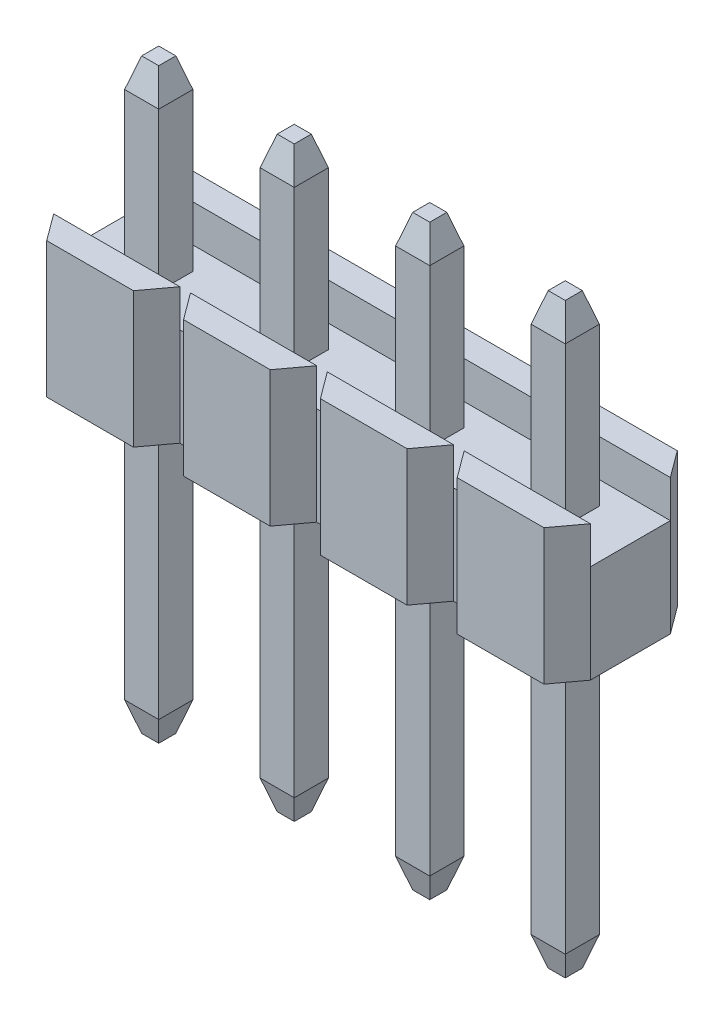
SolidWorks part; units mm, degrees
material "Plain Carbon Steel"
ref_plane "Front Plane" through (0, 0, 0) normal (0, 0, 1) x (1, 0, 0)
ref_plane "Top Plane" through (0, 0, 0) normal (0, 1, 0) x (1, 0, 0)
ref_plane "Right Plane" through (0, 0, 0) normal (1, 0, 0) x (0, 0, -1)
sketch "Sketch1" plane through (0, 0, 0) normal (0, 1, 0) x (1, 0, 0)
  line L0 (-4.66, -1.25) -> (-3.035, -1.25)
  line L1 (-3.035, -1.25) -> (-2.665, -0.75)
  line L2 (-2.665, -0.75) -> (-2.465, -0.75)
  line L3 (-2.465, -0.75) -> (-2.095, -1.25)
  line L4 (-2.095, -1.25) -> (-0.47, -1.25)
  line L5 (-0.47, -1.25) -> (-0.1, -0.75)
  line L6 (-0.1, -0.75) -> (0.1, -0.75)
  line L7 (0.1, -0.75) -> (0.47, -1.25)
  line L8 (0.47, -1.25) -> (2.095, -1.25)
  line L9 (2.095, -1.25) -> (2.465, -0.75)
  line L10 (2.465, -0.75) -> (2.665, -0.75)
  line L11 (2.665, -0.75) -> (3.035, -1.25)
  line L12 (3.035, -1.25) -> (4.66, -1.25)
  line L13 (4.66, -1.25) -> (5.03, -0.75)
  line L14 (5.03, -0.75) -> (5.03, 0.75)
  line L15 (5.03, 0.75) -> (4.66, 1.25)
  line L16 (4.66, 1.25) -> (3.035, 1.25)
  line L17 (3.035, 1.25) -> (2.665, 0.75)
  line L18 (2.665, 0.75) -> (2.465, 0.75)
  line L19 (2.465, 0.75) -> (2.095, 1.25)
  line L20 (2.095, 1.25) -> (0.47, 1.25)
  line L21 (0.47, 1.25) -> (0.1, 0.75)
  line L22 (0.1, 0.75) -> (-0.1, 0.75)
  line L23 (-0.1, 0.75) -> (-0.47, 1.25)
  line L24 (-0.47, 1.25) -> (-2.095, 1.25)
  line L25 (-2.095, 1.25) -> (-2.465, 0.75)
  line L26 (-2.465, 0.75) -> (-2.665, 0.75)
  line L27 (-2.665, 0.75) -> (-3.035, 1.25)
  line L28 (-3.035, 1.25) -> (-4.66, 1.25)
  line L29 (-4.66, 1.25) -> (-5.03, 0.75)
  line L30 (-5.03, 0.75) -> (-5.03, -0.75)
  line L31 (-5.03, -0.75) -> (-4.66, -1.25)
  line L32 (0, 2.3336) -> (0, 0) construction
  line L33 (0, 0) -> (6.1316, 0) construction
  dimension "D1" = 2.5
  dimension "D2" = 10.06
  dimension "D3" = 36.5
  dimension "D4" = 1.5
  dimension "D5" = 0.2
extrude "Boss-Extrude1" add sketch "Sketch1" against normal blind 2.54
sketch "Sketch5" plane through (0, 0, 0) normal (0, 1, 0) x (1, 0, 0)
  line L0 (2.665, 0.75) -> (2.465, 0.75) construction
  line L1 (-5.03, 0.75) -> (5.03, 0.75)
  line L2 (-5.03, 0.75) -> (-5.03, -0.75)
  line L3 (-5.03, -0.75) -> (5.03, -0.75)
  line L4 (5.03, 0.75) -> (5.03, -0.75)
  line L5 (2.465, -0.75) -> (2.665, -0.75) construction
  line L6 (5.03, -0.75) -> (5.03, 0.75) construction
  line L7 (-5.03, 0.75) -> (-5.03, -0.75) construction
extrude "Cut-Extrude3" cut sketch "Sketch5" against normal blind 0.7
sketch "Sketch3" plane through (0, -2.54, 0) normal (0, -1, 0) x (-1, 0, 0)
  line L0 (-4.13, 0.32) -> (-4.13, -0.32)
  line L1 (-4.13, -0.32) -> (-3.49, -0.32)
  line L2 (-3.49, -0.32) -> (-3.49, 0.32)
  line L3 (-3.49, 0.32) -> (-4.13, 0.32)
  line L4 (-1.59, 0.32) -> (-1.59, -0.32)
  line L5 (-1.59, -0.32) -> (-0.95, -0.32)
  line L6 (-0.95, -0.32) -> (-0.95, 0.32)
  line L7 (-0.95, 0.32) -> (-1.59, 0.32)
  line L8 (0.95, 0.32) -> (0.95, -0.32)
  line L9 (0.95, -0.32) -> (1.59, -0.32)
  line L10 (1.59, -0.32) -> (1.59, 0.32)
  line L11 (1.59, 0.32) -> (0.95, 0.32)
  line L12 (3.49, 0.32) -> (3.49, -0.32)
  line L13 (3.49, -0.32) -> (4.13, -0.32)
  line L14 (4.13, -0.32) -> (4.13, 0.32)
  line L15 (4.13, 0.32) -> (3.49, 0.32)
  line L16 (0, 2.1236) -> (0, 0) construction
  line L17 (0, 0) -> (5.9291, 0) construction
  line L18 (-4.13, -0.32) -> (-3.49, 0.32) construction
  dimension "D1" = 0.64
  dimension "D2" = 7.62
  dimension "D3" = 2.54
extrude "Cut-Extrude2" cut sketch "Sketch3" against normal through all
sketch "Sketch4" plane through (0, 0, 0) normal (0, -1, 0) x (1, 0, 0)
  line L5 (3.49, -0.32) -> (4.13, -0.32)
  line L6 (4.13, -0.32) -> (4.13, 0.32)
  line L7 (4.13, 0.32) -> (3.49, 0.32)
  line L8 (3.49, 0.32) -> (3.49, -0.32)
  line L9 (3.49, -0.32) -> (4.13, -0.32)
  line L10 (4.13, -0.32) -> (4.13, 0.32)
  line L11 (4.13, 0.32) -> (3.49, 0.32)
  line L12 (3.49, 0.32) -> (3.49, -0.32)
  line L14 (0.95, -0.32) -> (1.59, -0.32)
  line L15 (1.59, -0.32) -> (1.59, 0.32)
  line L16 (1.59, 0.32) -> (0.95, 0.32)
  line L17 (0.95, 0.32) -> (0.95, -0.32)
  line L18 (0.95, -0.32) -> (1.59, -0.32)
  line L19 (1.59, -0.32) -> (1.59, 0.32)
  line L20 (1.59, 0.32) -> (0.95, 0.32)
  line L21 (0.95, 0.32) -> (0.95, -0.32)
  line L23 (-1.59, -0.32) -> (-0.95, -0.32)
  line L24 (-0.95, -0.32) -> (-0.95, 0.32)
  line L25 (-0.95, 0.32) -> (-1.59, 0.32)
  line L26 (-1.59, 0.32) -> (-1.59, -0.32)
  line L27 (-1.59, -0.32) -> (-0.95, -0.32)
  line L28 (-0.95, -0.32) -> (-0.95, 0.32)
  line L29 (-0.95, 0.32) -> (-1.59, 0.32)
  line L30 (-1.59, 0.32) -> (-1.59, -0.32)
  line L32 (-4.13, -0.32) -> (-3.49, -0.32)
  line L33 (-3.49, -0.32) -> (-3.49, 0.32)
  line L34 (-3.49, 0.32) -> (-4.13, 0.32)
  line L35 (-4.13, 0.32) -> (-4.13, -0.32)
  line L36 (-4.13, -0.32) -> (-3.49, -0.32)
  line L37 (-3.49, -0.32) -> (-3.49, 0.32)
  line L38 (-3.49, 0.32) -> (-4.13, 0.32)
  line L39 (-4.13, 0.32) -> (-4.13, -0.32)
  dimension "D1" = 0
  dimension "D2" = 0
  dimension "D3" = 0
  dimension "D4" = 0
extrude "Boss-Extrude2" add sketch "Sketch4" against normal blind 2.8 and the other way blind 8.2
chamfer "Chamfer1" distance 0.16 angle 73.662 16 edges at (-3.81, -8.2, 0.32) (-3.49, -8.2, 0) (-3.81, -8.2, -0.32) (-4.13, -8.2, 0) (-1.27, -8.2, 0.32) (-0.95, -8.2, 0) (-1.27, -8.2, -0.32) (-1.59, -8.2, 0) (1.27, -8.2, 0.32) (1.59, -8.2, 0) (1.27, -8.2, -0.32) (0.95, -8.2, 0) (3.81, -8.2, 0.32) (4.13, -8.2, 0) (3.81, -8.2, -0.32) (3.49, -8.2, 0)
chamfer "Chamfer2" distance 0.16 angle 73.662 16 edges at (-3.81, 2.8, -0.32) (-3.49, 2.8, 0) (-3.81, 2.8, 0.32) (-4.13, 2.8, 0) (-1.27, 2.8, -0.32) (-0.95, 2.8, 0) (-1.27, 2.8, 0.32) (-1.59, 2.8, 0) (1.27, 2.8, -0.32) (1.59, 2.8, 0) (1.27, 2.8, 0.32) (0.95, 2.8, 0) (3.81, 2.8, -0.32) (4.13, 2.8, 0) (3.81, 2.8, 0.32) (3.49, 2.8, 0)
